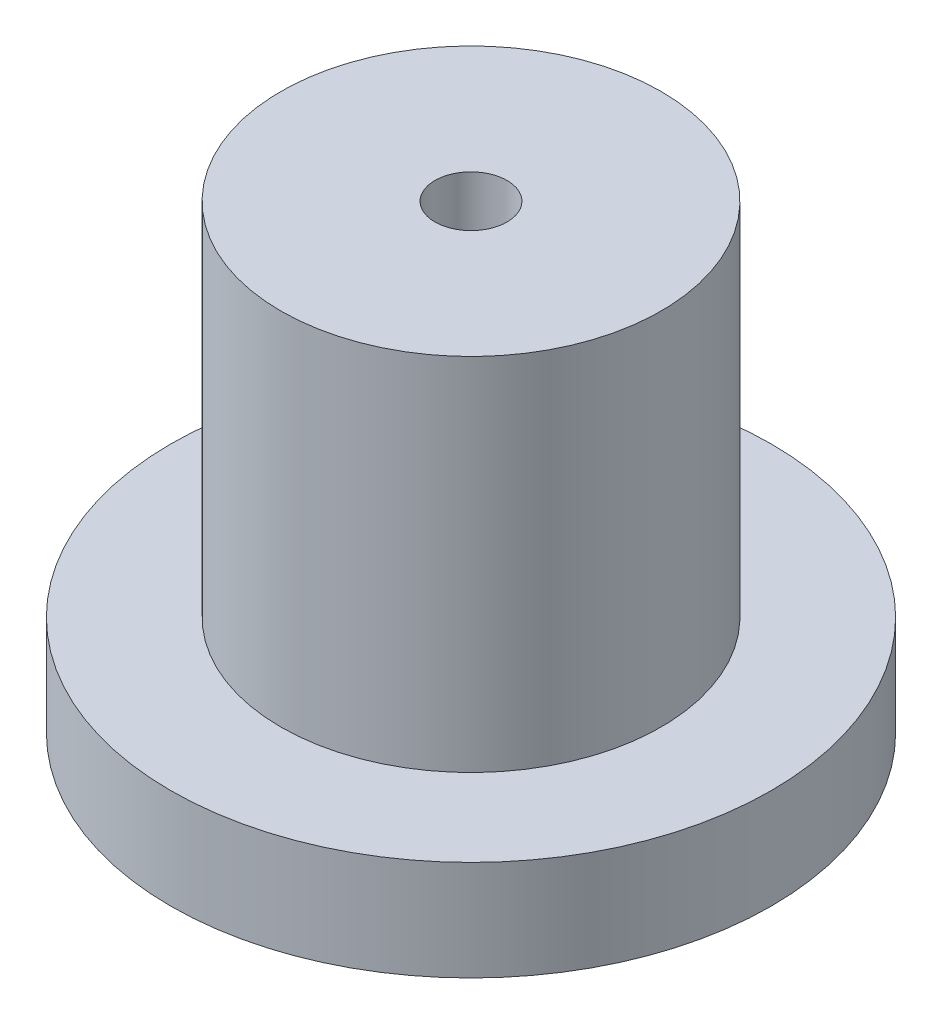
SolidWorks part; units mm, degrees
ref_plane "Front Plane" through (0, 0, 0) normal (0, 0, 1) x (1, 0, 0)
ref_plane "Top Plane" through (0, 0, 0) normal (0, 1, 0) x (1, 0, 0)
ref_plane "Right Plane" through (0, 0, 0) normal (1, 0, 0) x (0, 0, -1)
sketch "Sketch2" plane through (0, 0, 0) normal (0, 1, 0) x (1, 0, 0)
  circle A0 centre (0, 0) radius 15
  dimension "D1" = 30
extrude "Boss-Extrude1" add sketch "Sketch2" along normal blind 5
sketch "Sketch3" plane through (0, 5, 0) normal (0, 1, 0) x (1, 0, 0)
  circle A0 centre (0, 0) radius 9.5
  dimension "D1" = 19
extrude "Boss-Extrude2" add sketch "Sketch3" along normal blind 18
sketch "Sketch4" plane through (0, 0, 0) normal (0, -1, 0) x (1, 0, 0)
  circle A0 centre (0, 0) radius 7.5
  dimension "D1" = 15
extrude "Cut-Extrude1" cut sketch "Sketch4" against normal blind 18
sketch "Sketch5" plane through (0, 23, 0) normal (0, 1, 0) x (1, 0, 0)
  circle A0 centre (0, 0) radius 1.7
  point P0 (0, 0)
  dimension "D1" = 3.4
hole_wizard "M3 Clearance Hole1" positions "Sketch5" profile "Sketch7" hole size "M3" standard "ANSI Metric" end condition through all
sketch "Sketch7" plane through (0, 23, 0) normal (1, 0, 0) x (0, 0, 1)
  line L0 (0, 0) -> (0, 23)
  line L1 (0, 23) -> (1.8, 23)
  line L2 (1.8, 23) -> (1.8, 0)
  line L5 (1.8, 0) -> (0, 0)
  line L11 (0, -6.35) -> (0, 107.95) construction
  dimension "Thru Hole Dia." = 3.6
  dimension "Thru Hole Depth" = 23
